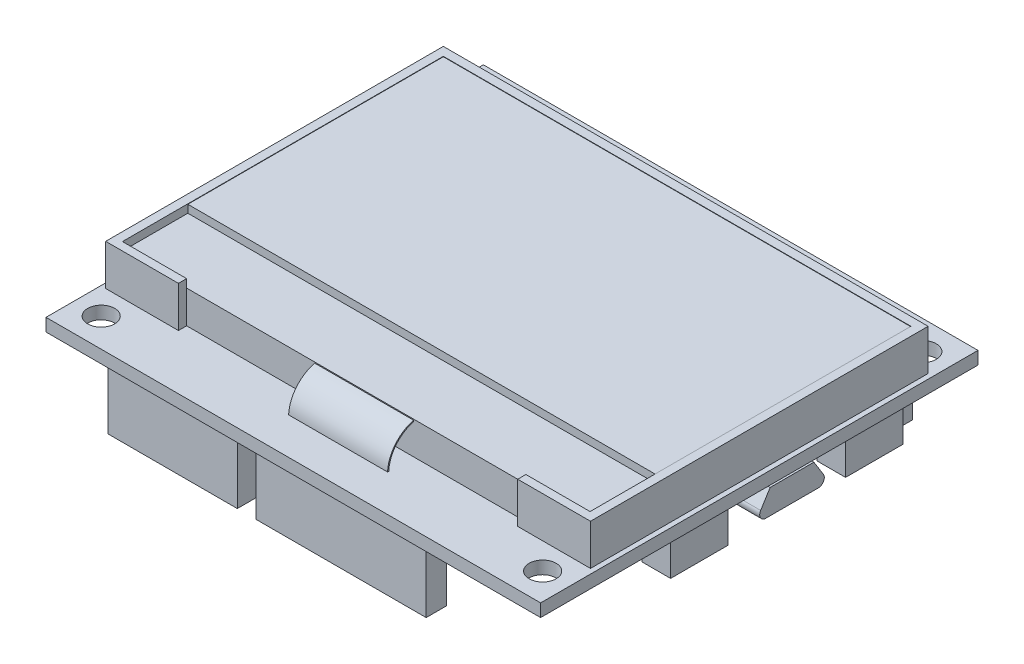
SolidWorks part; units mm, degrees
ref_plane "Front Plane" through (0, 0, 0) normal (0, 0, 1) x (1, 0, 0)
ref_plane "Top Plane" through (0, 0, 0) normal (0, 1, 0) x (1, 0, 0)
ref_plane "Right Plane" through (0, 0, 0) normal (1, 0, 0) x (0, 0, -1)
sketch "Sketch1" plane through (0, 0, 0) normal (0, 1, 0) x (1, 0, 0)
  line L0 (-27.9705, 29.6143) -> (-31.2205, 33.1143) construction
  line L1 (-31.2205, 33.1143) -> (29.2795, 33.1143)
  line L2 (-31.2205, 33.1143) -> (-31.2205, -20.3857)
  line L3 (-31.2205, -20.3857) -> (29.2795, -20.3857)
  line L4 (29.2795, 33.1143) -> (29.2795, -20.3857)
  line L5 (26.0295, 29.6143) -> (29.2795, 33.1143) construction
  line L6 (26.0295, -16.8857) -> (29.2795, -20.3857) construction
  line L7 (-27.9705, -16.8857) -> (-31.2205, -20.3857) construction
  circle A0 centre (-27.9705, -16.8857) radius 1.65
  circle A1 centre (-27.9705, 29.6143) radius 1.65
  circle A2 centre (26.0295, 29.6143) radius 1.65
  circle A3 centre (26.0295, -16.8857) radius 1.65
  dimension "D5" = 3.3
  dimension "D1" = 60.5
  dimension "D2" = 53.5
  dimension "D3" = 54
  dimension "D4" = 46.5
extrude "Boss-Extrude1" add sketch "Sketch1" along normal blind 1.56
sketch "Sketch2" plane through (0, 1.56, 0) normal (0, 1, 0) x (1, 0, 0)
  line L0 (29.2795, 33.1143) -> (-31.2205, 33.1143) construction
  line L1 (-30.6205, 27.6143) -> (28.6795, 27.6143)
  line L2 (-30.6205, 27.6143) -> (-30.6205, -13.6857)
  line L3 (-30.6205, -13.6857) -> (28.6795, -13.6857)
  line L4 (28.6795, 27.6143) -> (28.6795, -13.6857)
  point P6 (-0.9705, 27.6143)
  point P7 (-0.9705, 33.1143)
  dimension "D1" = 59.3
  dimension "D2" = 41.3
  dimension "D3" = 5.5
extrude "Boss-Extrude2" add sketch "Sketch2" along normal blind 5
sketch "Sketch4" plane through (0, 0, 13.6857) normal (0, 0, 1) x (1, 0, 0)
  line L0 (-30.6205, 6.56) -> (28.6795, 6.56) construction
  line L1 (19.7795, 6.56) -> (-21.7205, 6.56)
  line L2 (19.7795, 6.56) -> (19.7795, 1.56)
  line L3 (19.7795, 1.56) -> (-21.7205, 1.56)
  line L4 (-21.7205, 6.56) -> (-21.7205, 1.56)
  line L5 (-30.6205, 1.56) -> (28.6795, 1.56) construction
  point P8 (-0.9705, 6.56)
  point P10 (-0.9705, 6.56)
  dimension "D1" = 41.5
extrude "Cut-Extrude1" cut sketch "Sketch4" against normal blind 1
sketch "Sketch3" plane through (0, 0, 0) normal (1, 0, 0) x (0, 0, -1)
  line L0 (-11.6857, 5.41) -> (-11.6857, 5.56)
  line L1 (-15.8809, 1.56) -> (-15.7308, 1.56)
  line L2 (-20.3857, 1.56) -> (-20.3857, 0) construction
  line L3 (-13.6857, 6.56) -> (-13.6857, 1.56) construction
  line L5 (-20.3857, 1.56) -> (33.1143, 1.56) construction
  line L7 (-13.6857, 1.56) -> (27.6143, 1.56) construction
  arc A0 (-11.6857, 5.56) -> (-15.8809, 1.56) centre (-11.6857, 1.36) ccw
  arc A1 (-11.6857, 5.41) -> (-15.7308, 1.56) centre (-11.6857, 1.36) ccw
  point P4 (-15.8857, 1.36)
  point P7 (-11.6857, 5.41)
  point P12 (-15.7308, 1.56)
  point P15 (-11.6857, 5.56)
  dimension "D3" = 0.15
  dimension "D1" = 4.5
  dimension "D2" = 2
  dimension "D4" = 4
extrude "Boss-Extrude3" add sketch "Sketch3" along normal blind 6.05 and the other way blind 6.05
sketch "Sketch5" plane through (0, 0, 0) normal (0, -1, 0) x (-1, 0, 0)
  line L0 (31.2205, 33.1143) -> (31.2205, -20.3857) construction
  line L1 (25.0205, -18.9857) -> (9.2205, -18.9857)
  line L2 (25.0205, -18.9857) -> (25.0205, -16.4857)
  line L3 (25.0205, -16.4857) -> (9.2205, -16.4857)
  line L4 (9.2205, -18.9857) -> (9.2205, -16.4857)
  line L5 (6.9205, -18.9857) -> (-13.8795, -18.9857)
  line L6 (6.9205, -18.9857) -> (6.9205, -16.4857)
  line L7 (6.9205, -16.4857) -> (-13.8795, -16.4857)
  line L8 (-13.8795, -18.9857) -> (-13.8795, -16.4857)
  line L9 (25.0205, 29.2143) -> (4.2205, 29.2143)
  line L10 (25.0205, 29.2143) -> (25.0205, 31.7143)
  line L11 (25.0205, 31.7143) -> (4.2205, 31.7143)
  line L12 (4.2205, 29.2143) -> (4.2205, 31.7143)
  line L13 (3.2205, 29.2143) -> (-22.6795, 29.2143)
  line L14 (3.2205, 29.2143) -> (3.2205, 31.7143)
  line L15 (3.2205, 31.7143) -> (-22.6795, 31.7143)
  line L16 (-22.6795, 29.2143) -> (-22.6795, 31.7143)
  line L17 (25.0205, -16.4857) -> (25.0205, 29.2143) construction
  point P16 (6.9205, -17.7357)
  point P19 (25.0205, 6.3643)
  point P20 (31.2205, 6.3643)
  dimension "D1" = 2.5
  dimension "D2" = 2.5
  dimension "D3" = 2.5
  dimension "D4" = 2.5
  dimension "D5" = 15.8
  dimension "D6" = 20.8
  dimension "D7" = 20.8
  dimension "D8" = 25.9
  dimension "D9" = 1
  dimension "D10" = 2.3
  dimension "D11" = 48.2
  dimension "D12" = 6.2
extrude "Boss-Extrude4" add sketch "Sketch5" along normal blind 8.4
sketch "Sketch6" plane through (0, 0, 0) normal (0, -1, 0) x (1, 0, 0)
  line L0 (-31.2205, -33.1143) -> (-31.2205, 20.3857) construction
  line L1 (-31.0205, 4.2857) -> (-27.5205, 4.2857)
  line L2 (-31.0205, 4.2857) -> (-31.0205, -2.7143)
  line L3 (-31.0205, -2.7143) -> (-27.5205, -2.7143)
  line L4 (-27.5205, 4.2857) -> (-27.5205, -2.7143)
  line L5 (-31.0205, -17.1143) -> (-27.5205, -17.1143)
  line L6 (-31.0205, -17.1143) -> (-31.0205, -24.1143)
  line L7 (-31.0205, -24.1143) -> (-27.5205, -24.1143)
  line L8 (-27.5205, -17.1143) -> (-27.5205, -24.1143)
  line L9 (25.5795, 4.2857) -> (29.0795, 4.2857)
  line L10 (25.5795, 4.2857) -> (25.5795, -2.7143)
  line L11 (25.5795, -2.7143) -> (29.0795, -2.7143)
  line L12 (29.0795, 4.2857) -> (29.0795, -2.7143)
  line L13 (25.5795, -17.1143) -> (29.0795, -17.1143)
  line L14 (25.5795, -17.1143) -> (25.5795, -24.1143)
  line L15 (25.5795, -24.1143) -> (29.0795, -24.1143)
  line L16 (29.0795, -17.1143) -> (29.0795, -24.1143)
  line L17 (29.2795, 20.3857) -> (29.2795, -33.1143) construction
  circle A0 centre (-27.9705, 16.8857) radius 1.65 construction
  circle A1 centre (-27.9705, -29.6143) radius 1.65 construction
  dimension "D1" = 7
  dimension "D2" = 3.5
  dimension "D3" = 12.6
  dimension "D4" = 5.5
  dimension "D5" = 0.2
  dimension "D6" = 0.2
extrude "Boss-Extrude5" add sketch "Sketch6" along normal blind 4
sketch "Sketch7" plane through (0, 6.56, 0) normal (0, 1, 0) x (1, 0, 0)
  line L0 (-30.6205, 27.6143) -> (-30.6205, -13.6857) construction
  line L1 (-29.5705, -4.6857) -> (27.6295, -4.6857)
  line L2 (-29.5705, -4.6857) -> (-29.5705, -12.6857)
  line L3 (-29.5705, -12.6857) -> (27.6295, -12.6857)
  line L4 (27.6295, -4.6857) -> (27.6295, -12.6857)
  line L5 (-30.6205, -13.6857) -> (-21.7205, -13.6857) construction
  dimension "D1" = 57.2
  dimension "D2" = 8
  dimension "D3" = 1.05
  dimension "D4" = 1
extrude "Cut-Extrude2" cut sketch "Sketch7" against normal blind 1
sketch "Sketch8" plane through (0, 6.56, 0) normal (0, 1, 0) x (1, 0, 0)
  line L0 (27.6295, -12.6857) -> (27.6295, -4.6857) construction
  line L1 (-29.5705, -4.6857) -> (27.6295, -4.6857)
  line L2 (-29.5705, -4.6857) -> (-29.5705, 26.5643)
  line L3 (-29.5705, 26.5643) -> (27.6295, 26.5643)
  line L4 (27.6295, -4.6857) -> (27.6295, 26.5643)
  line L5 (28.6795, 27.6143) -> (-30.6205, 27.6143) construction
  dimension "D1" = 1.05
extrude "Cut-Extrude3" cut sketch "Sketch8" against normal blind 0.05
sketch "Sketch9" plane through (0, 0, 0) normal (0, -1, 0) x (-1, 0, 0)
  line L1 (-29.5295, 6.1143) -> (-23.9295, 6.1143)
  line L2 (-29.5295, 6.1143) -> (-29.5295, 14.1143)
  line L3 (-29.5295, 14.1143) -> (-23.9295, 14.1143)
  line L4 (-23.9295, 6.1143) -> (-23.9295, 14.1143)
  line L5 (-29.2795, -20.3857) -> (-29.2795, 33.1143) construction
  circle A0 centre (-26.0295, -16.8857) radius 1.65 construction
  point P4 (0, 0)
  point P6 (-29.5295, 10.1143)
  point P9 (0, 0)
  dimension "D1" = 8
  dimension "D2" = 5.6
  dimension "D3" = 27
  dimension "D4" = 0.25
extrude "Boss-Extrude6" add sketch "Sketch9" along normal blind 3
sketch "Sketch10" plane through (29.5295, 0, 0) normal (1, 0, 0) x (0, 0, -1)
  line L0 (14.1143, -3) -> (6.1143, -3) construction
  line L4 (14.1143, 0) -> (6.1143, 0) construction
  line L5 (7.4364, 0) -> (6.2783, -1.8524)
  line L6 (12.7922, 0) -> (13.9502, -1.8524)
  line L8 (14.1143, -3) -> (14.1143, 0) construction
  line L9 (6.1143, -3) -> (6.1143, 0) construction
  line L10 (7.4364, 0) -> (6.1143, 0)
  line L11 (6.1143, 0) -> (6.1143, -3)
  line L12 (6.1143, -3) -> (6.9143, -3)
  line L13 (13.3143, -3) -> (14.1143, -3)
  line L14 (14.1143, -3) -> (14.1143, 0)
  line L15 (14.1143, 0) -> (12.7922, 0)
  arc A0 (6.2783, -1.8524) -> (6.9143, -3) centre (6.9143, -2.25) ccw
  arc A1 (13.3143, -3) -> (13.9502, -1.8524) centre (13.3143, -2.25) ccw
  dimension "D1" = 1.5
  dimension "D2" = 0.8
  dimension "D3" = 0.8
extrude "Cut-Extrude4" cut sketch "Sketch10" against normal up to surface (5.6 mm away) up to face at (23.9295, -1.5, -10.1143)
